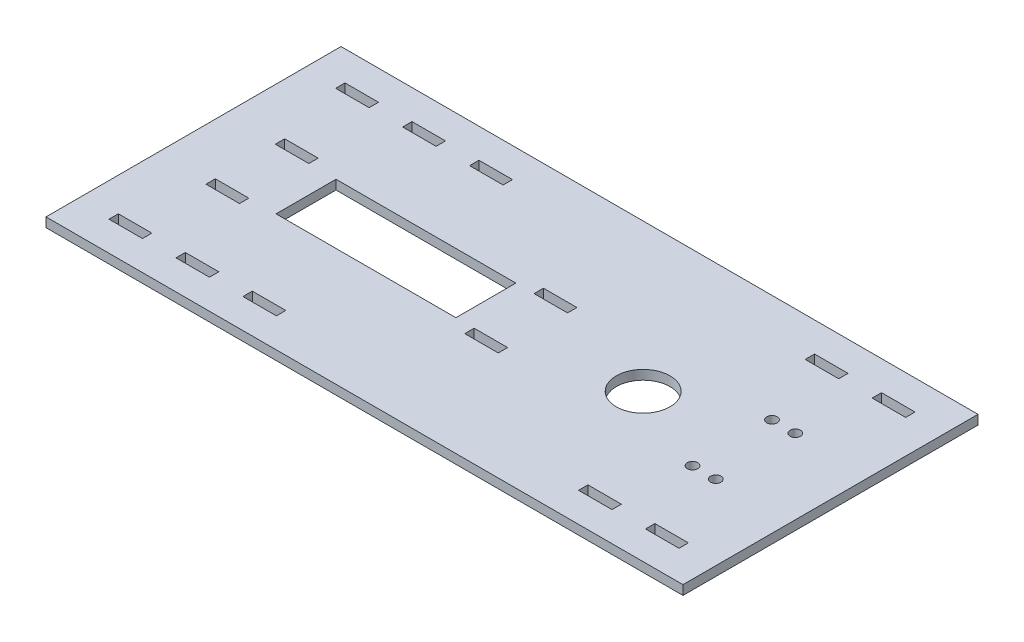
SolidWorks part; units mm, degrees
ref_plane "Front Plane" through (0, 0, 0) normal (0, 0, 1) x (1, 0, 0)
ref_plane "Top Plane" through (0, 0, 0) normal (0, 1, 0) x (1, 0, 0)
ref_plane "Right Plane" through (0, 0, 0) normal (1, 0, 0) x (0, 0, -1)
sketch "Sketch1" plane through (0, 0, 0) normal (0, 1, 0) x (1, 0, 0)
  line L1 (-109.2058, 67.4639) -> (106.6942, 67.4639)
  line L2 (-109.2058, 67.4639) -> (-109.2058, -32.5361)
  line L3 (-109.2058, -32.5361) -> (106.6942, -32.5361)
  line L4 (106.6942, 67.4639) -> (106.6942, -32.5361)
  dimension "D1" = 100
  dimension "D2" = 215.9
extrude "Boss-Extrude1" add sketch "Sketch1" along normal blind 3.175
sketch "Sketch3" plane through (0, 3.175, 0) normal (0, 1, 0) x (1, 0, 0)
  line L0 (106.6942, 67.4639) -> (-109.2058, 67.4639) construction
  line L1 (-97.8558, 57.4639) -> (-86.5058, 57.4639)
  line L2 (-97.8558, 57.4639) -> (-97.8558, 54.2889)
  line L3 (-97.8558, 54.2889) -> (-86.5058, 54.2889)
  line L4 (-86.5058, 57.4639) -> (-86.5058, 54.2889)
  line L5 (-109.2058, 67.4639) -> (-109.2058, -32.5361) construction
  line L6 (-52.4558, 57.4639) -> (-41.1058, 57.4639)
  line L7 (-75.1558, 57.4639) -> (-63.8058, 57.4639)
  line L8 (-75.1558, 57.4639) -> (-75.1558, 54.2889)
  line L9 (-75.1558, 54.2889) -> (-63.8058, 54.2889)
  line L10 (-63.8058, 57.4639) -> (-63.8058, 54.2889)
  line L11 (-52.4558, 57.4639) -> (-52.4558, 54.2889)
  line L12 (-52.4558, 54.2889) -> (-41.1058, 54.2889)
  line L13 (-41.1058, 57.4639) -> (-41.1058, 54.2889)
  line L14 (61.2942, 57.4639) -> (72.6442, 57.4639)
  line L15 (61.2942, 57.4639) -> (61.2942, 54.2889)
  line L16 (61.2942, 54.2889) -> (72.6442, 54.2889)
  line L17 (72.6442, 57.4639) -> (72.6442, 54.2889)
  line L18 (106.6942, -32.5361) -> (106.6942, 67.4639) construction
  line L19 (83.9942, 57.4639) -> (95.3442, 57.4639)
  line L20 (83.9942, 57.4639) -> (83.9942, 54.2889)
  line L21 (83.9942, 54.2889) -> (95.3442, 54.2889)
  line L22 (95.3442, 57.4639) -> (95.3442, 54.2889)
  point P26 (72.6442, 55.8764)
  point P27 (83.9942, 55.8764)
  dimension "D1" = 10
  dimension "D2" = 11.35
  dimension "D3" = 11.35
  dimension "D4" = 11.35
  dimension "D5" = 11.35
  dimension "D6" = 3.175
  dimension "D7" = 11.35
  dimension "D8" = 11.35
  dimension "D9" = 11.35
  dimension "D10" = 3.175
  dimension "D11" = 11.35
  dimension "D12" = 11.35
extrude "Cut-Extrude2" cut sketch "Sketch3" against normal blind 3.175
sketch "Sketch4" plane through (0, 3.175, 0) normal (0, 1, 0) x (1, 0, 0)
  line L0 (-109.2058, -32.5361) -> (106.6942, -32.5361) construction
  line L1 (-97.8558, -19.3611) -> (-86.5058, -19.3611)
  line L2 (-97.8558, -19.3611) -> (-97.8558, -22.5361)
  line L3 (-97.8558, -22.5361) -> (-86.5058, -22.5361)
  line L4 (-86.5058, -19.3611) -> (-86.5058, -22.5361)
  line L5 (-109.2058, 67.4639) -> (-109.2058, -32.5361) construction
  line L6 (106.6942, -32.5361) -> (106.6942, 67.4639) construction
  line L7 (-75.1558, -19.3611) -> (-63.8058, -19.3611)
  line L8 (-75.1558, -19.3611) -> (-75.1558, -22.5361)
  line L9 (-75.1558, -22.5361) -> (-63.8058, -22.5361)
  line L10 (-63.8058, -19.3611) -> (-63.8058, -22.5361)
  line L11 (-52.4558, -19.3611) -> (-41.1058, -19.3611)
  line L12 (-52.4558, -19.3611) -> (-52.4558, -22.5361)
  line L13 (-52.4558, -22.5361) -> (-41.1058, -22.5361)
  line L14 (-41.1058, -19.3611) -> (-41.1058, -22.5361)
  line L15 (61.2942, -19.3611) -> (72.6442, -19.3611)
  line L16 (61.2942, -19.3611) -> (61.2942, -22.5361)
  line L17 (61.2942, -22.5361) -> (72.6442, -22.5361)
  line L18 (72.6442, -19.3611) -> (72.6442, -22.5361)
  line L19 (83.9942, -19.3611) -> (95.3442, -19.3611)
  line L20 (83.9942, -19.3611) -> (83.9942, -22.5361)
  line L21 (83.9942, -22.5361) -> (95.3442, -22.5361)
  line L22 (95.3442, -19.3611) -> (95.3442, -22.5361)
  line L23 (-97.8558, 54.2889) -> (-86.5058, 54.2889) construction
  point P6 (-97.8558, -20.9486)
  dimension "D1" = 10
  dimension "D2" = 11.35
  dimension "D3" = 11.35
  dimension "D4" = 3.175
  dimension "D5" = 11.35
  dimension "D6" = 11.35
  dimension "D7" = 11.35
  dimension "D8" = 11.35
  dimension "D9" = 11.35
  dimension "D10" = 11.35
  dimension "D11" = 11.35
  dimension "D12" = 11.35
  dimension "D13" = 73.65
extrude "Cut-Extrude3" cut sketch "Sketch4" against normal blind 3.175
sketch "Sketch5" plane through (0, 3.175, 0) normal (0, 1, 0) x (1, 0, 0)
  line L0 (-109.2058, 67.4639) -> (-109.2058, -32.5361) construction
  line L1 (-71.1058, 27.6639) -> (-10.1458, 27.6639)
  line L2 (-71.1058, 27.6639) -> (-71.1058, 7.3439)
  line L3 (-71.1058, 7.3439) -> (-10.1458, 7.3439)
  line L4 (-10.1458, 27.6639) -> (-10.1458, 7.3439)
  line L7 (106.6942, 67.4639) -> (-109.2058, 67.4639) construction
  dimension "D1" = 38.1
  dimension "D2" = 20.32
  dimension "D3" = 39.8
  dimension "D4" = 60.96
extrude "Cut-Extrude4" cut sketch "Sketch5" against normal blind 3.175 and the other way through all
sketch "Sketch7" plane through (0, 3.175, 0) normal (0, 1, 0) x (1, 0, 0)
  line L0 (106.6942, 67.4639) -> (-109.2058, 67.4639) construction
  line L1 (106.6942, -32.5361) -> (106.6942, 67.4639) construction
  circle A0 centre (43.1942, 17.4639) radius 9.1
  dimension "D1" = 50
  dimension "D2" = 63.5
extrude "Cut-Extrude6" cut sketch "Sketch7" against normal blind 3.175
sketch "Sketch8" plane through (0, 3.175, 0) normal (0, 1, 0) x (1, 0, 0)
  line L0 (-109.2058, -32.5361) -> (106.6942, -32.5361) construction
  line L1 (106.6942, -32.5361) -> (106.6942, 67.4639) construction
  circle A0 centre (73.3948, 30.9385) radius 1.778
  circle A1 centre (81.2942, 3.9891) radius 1.778
  circle A2 centre (73.3948, 3.9891) radius 1.778
  circle A3 centre (81.2942, 30.9385) radius 1.778
  dimension "D1" = 26.9494
  dimension "D2" = 7.8994
  dimension "D3" = 36.5252
  dimension "D4" = 25.4
extrude "Cut-Extrude7" cut sketch "Sketch8" against normal blind 3.175
sketch "Sketch9" plane through (0, 3.175, 0) normal (0, 1, 0) x (1, 0, 0)
  line L0 (-91.6798, 7.3439) -> (-80.3298, 7.3439)
  line L1 (-91.6798, 7.3439) -> (-91.6798, 4.1689)
  line L2 (-91.6798, 4.1689) -> (-80.3298, 4.1689)
  line L3 (-80.3298, 7.3439) -> (-80.3298, 4.1689)
  line L4 (-91.6798, 30.8389) -> (-80.3298, 30.8389)
  line L5 (-91.6798, 30.8389) -> (-91.6798, 27.6639)
  line L6 (-91.6798, 27.6639) -> (-80.3298, 27.6639)
  line L7 (-80.3298, 30.8389) -> (-80.3298, 27.6639)
  line L8 (-3.9698, 7.3439) -> (7.3802, 7.3439)
  line L9 (-3.9698, 7.3439) -> (-3.9698, 4.1689)
  line L10 (-3.9698, 4.1689) -> (7.3802, 4.1689)
  line L11 (7.3802, 7.3439) -> (7.3802, 4.1689)
  line L12 (-3.9698, 30.8389) -> (7.3802, 30.8389)
  line L13 (-3.9698, 30.8389) -> (-3.9698, 27.6639)
  line L14 (-3.9698, 27.6639) -> (7.3802, 27.6639)
  line L15 (7.3802, 30.8389) -> (7.3802, 27.6639)
  line L16 (-71.1058, 27.6639) -> (-10.1458, 27.6639) construction
  line L17 (-109.2058, 67.4639) -> (-109.2058, -32.5361) construction
  line L18 (-71.1058, 7.3439) -> (-71.1058, 27.6639) construction
  dimension "D1" = 11.35
  dimension "D2" = 11.35
  dimension "D3" = 99.06
  dimension "D4" = 11.35
  dimension "D5" = 17.526
  dimension "D6" = 11.35
  dimension "D7" = 20.574
extrude "Cut-Extrude8" cut sketch "Sketch9" against normal blind 3.175
